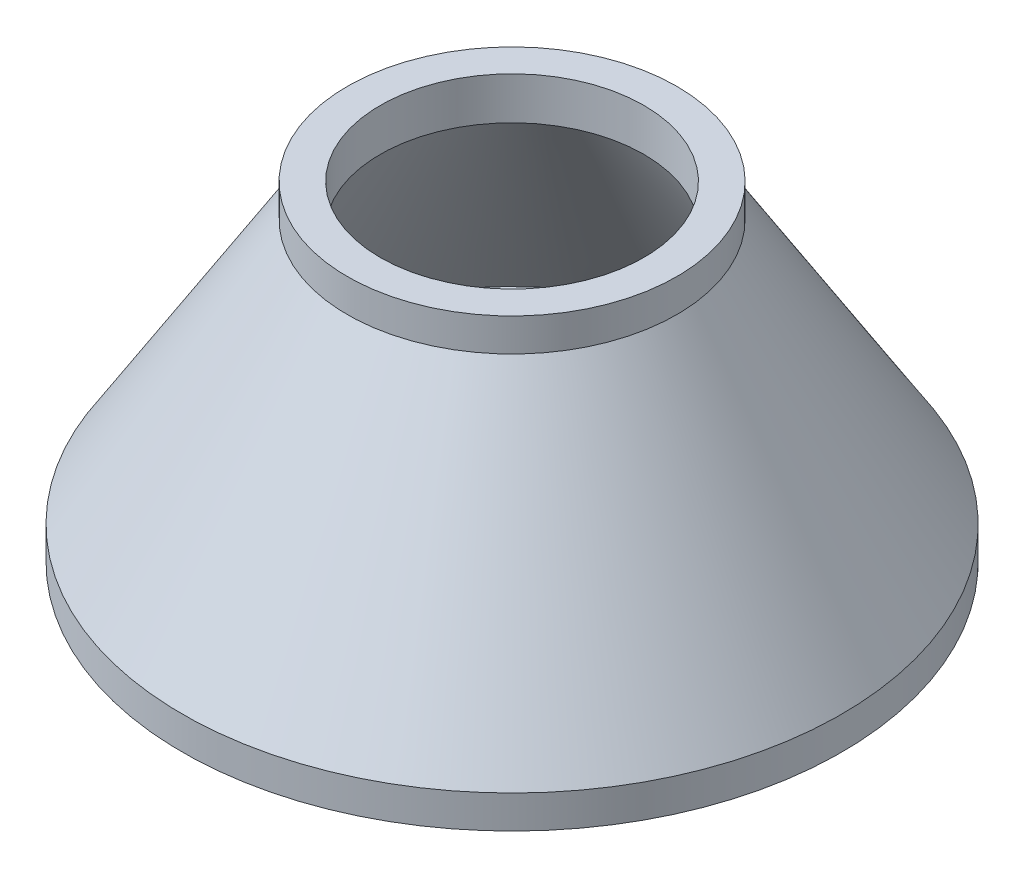
SolidWorks part; units mm, degrees
material "ABS"
ref_plane "Front Plane" through (0, 0, 0) normal (0, 0, 1) x (1, 0, 0)
ref_plane "Top Plane" through (0, 0, 0) normal (0, 1, 0) x (1, 0, 0)
ref_plane "Right Plane" through (0, 0, 0) normal (1, 0, 0) x (0, 0, -1)
sketch "Sketch2" plane through (0, 0, 0) normal (0, 0, 1) x (1, 0, 0)
  line L0 (0, 0) -> (0, 149.3905) construction
  line L1 (0, 0) -> (100, 0)
  line L2 (100, 0) -> (100, 10)
  line L3 (100, 10) -> (50, 90)
  line L4 (50, 90) -> (50, 100)
  line L5 (50, 100) -> (0, 100)
  line L6 (0, 0) -> (0, 100)
  dimension "D1" = 100
  dimension "D2" = 10
  dimension "D3" = 100
  dimension "D4" = 50
revolve "Revolve1" add sketch "Sketch2" angle 360 about L0
shell "Shell1" thickness 10
ref_point "O"
